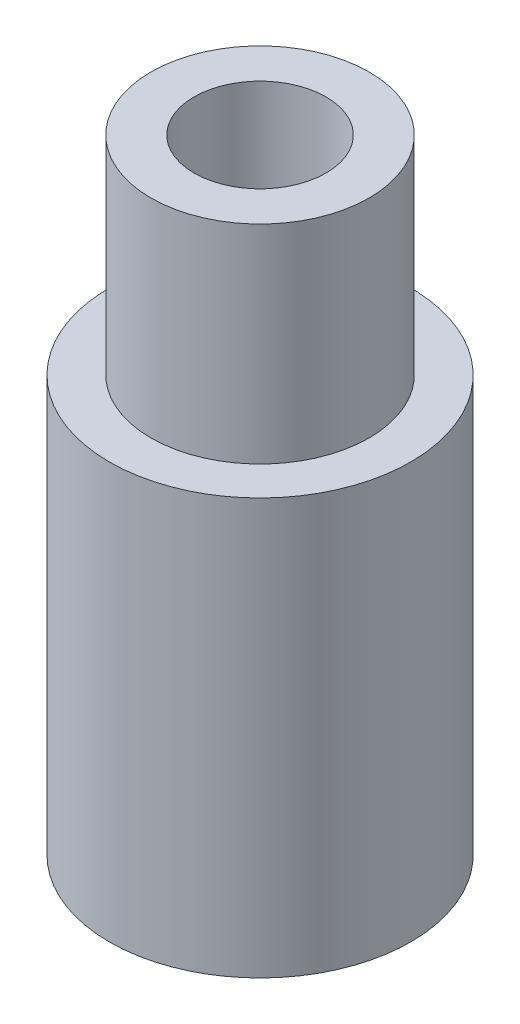
SolidWorks part; units mm, degrees
ref_plane "Front Plane" through (0, 0, 0) normal (0, 0, 1) x (1, 0, 0)
ref_plane "Top Plane" through (0, 0, 0) normal (0, 1, 0) x (1, 0, 0)
ref_plane "Right Plane" through (0, 0, 0) normal (1, 0, 0) x (0, 0, -1)
sketch "Sketch1" plane through (0, 0, 0) normal (0, 1, 0) x (1, 0, 0)
  circle A0 centre (0, 0) radius 3.175
  circle A1 centre (0, 0) radius 7.25
  dimension "D1" = 6.35
  dimension "D2" = 14.5
extrude "Boss-Extrude1" add sketch "Sketch1" along normal blind 30
sketch "Sketch2" plane through (0, 30, 0) normal (0, 1, 0) x (1, 0, 0)
  circle A0 centre (0, 0) radius 5.25
  dimension "D1" = 10.5
extrude "Cut-Extrude1" cut sketch "Sketch2" against normal blind 10 flip side to cut
sketch "Sketch3" plane through (0, 0, 0) normal (0, -1, 0) x (1, 0, 0)
  circle A1 centre (0, 0) radius 5.25
  dimension "D1" = 10.5
extrude "Cut-Extrude2" cut sketch "Sketch3" against normal blind 10
